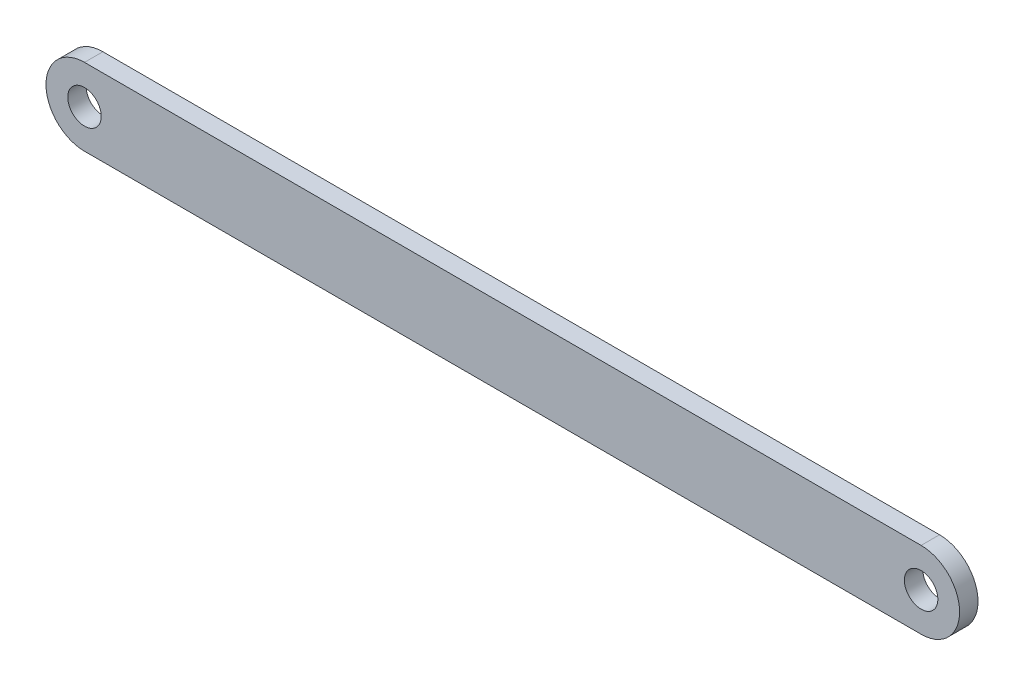
SolidWorks part; units mm, degrees
material "1.0490 (S275N)"
ref_plane "Front Plane" through (0, 0, 0) normal (0, 0, 1) x (1, 0, 0)
ref_plane "Top Plane" through (0, 0, 0) normal (0, 1, 0) x (1, 0, 0)
ref_plane "Right Plane" through (0, 0, 0) normal (1, 0, 0) x (0, 0, -1)
sketch "Sketch1" plane through (0, 0, 0) normal (0, 0, 1) x (1, 0, 0)
  line L0 (-125, 0) -> (125, 0) construction
  line L1 (-125, 11.5) -> (125, 11.5)
  line L2 (-125, -11.5) -> (125, -11.5)
  arc A0 (-125, 11.5) -> (-125, -11.5) centre (-125, 0) ccw
  arc A1 (125, -11.5) -> (125, 11.5) centre (125, 0) ccw
  circle A2 centre (-125, 0) radius 5
  circle A3 centre (125, 0) radius 5
  point P3 (0, 0)
  dimension "D2" = 23
  dimension "D3" = 10
  dimension "D4" = 10
  dimension "D1" = 250
  dimension "D5" = 125
extrude "link_CD_JH" add sketch "Sketch1" along normal mid plane 5.5
